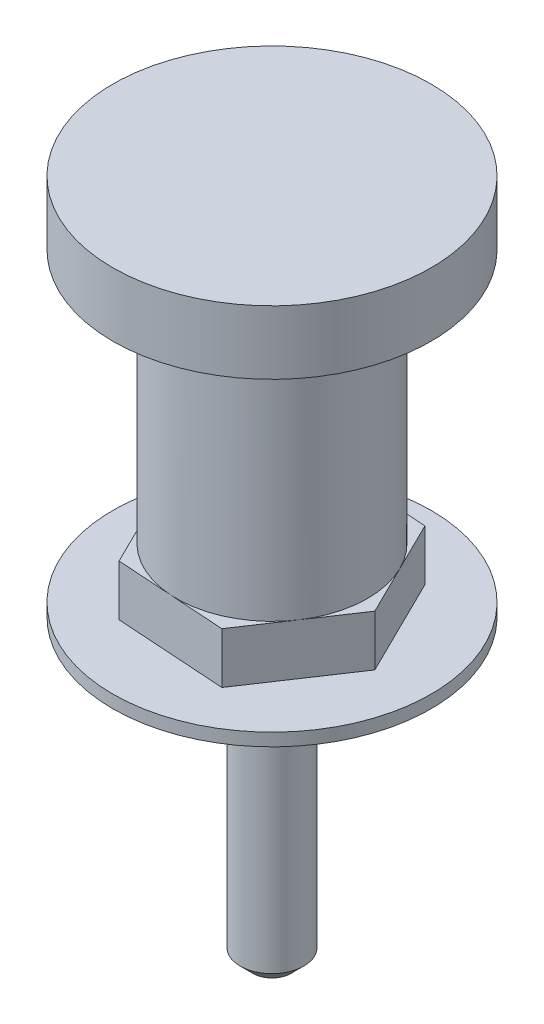
SolidWorks part; units mm, degrees
ref_plane "Front Plane" through (0, 0, 0) normal (0, 0, 1) x (1, 0, 0)
ref_plane "Top Plane" through (0, 0, 0) normal (0, 1, 0) x (1, 0, 0)
ref_plane "Right Plane" through (0, 0, 0) normal (1, 0, 0) x (0, 0, -1)
sketch "Sketch1" plane through (0, 0, 0) normal (0, 1, 0) x (1, 0, 0)
  circle A0 centre (0, 0) radius 12.5
  dimension "D1" = 25
extrude "Boss-Extrude1" add sketch "Sketch1" along normal blind 1
sketch "Sketch2" plane through (0, 1, 0) normal (0, 1, 0) x (1, 0, 0)
  line L1 (3.8307, -7.767) -> (8.6417, -0.566)
  line L2 (8.6417, -0.566) -> (4.8111, 7.2009)
  line L3 (4.8111, 7.2009) -> (-3.8307, 7.767)
  line L4 (-3.8307, 7.767) -> (-8.6417, 0.566)
  line L5 (-8.6417, 0.566) -> (-4.8111, -7.2009)
  line L6 (-4.8111, -7.2009) -> (3.8307, -7.767)
  circle A0 centre (0, 0) radius 7.5 construction
  dimension "D1" = 15
extrude "Boss-Extrude2" add sketch "Sketch2" along normal blind 4
sketch "Sketch4" plane through (0, 5, 0) normal (0, 1, 0) x (1, 0, 0)
  circle A0 centre (0, 0) radius 2.5
  dimension "D1" = 5
extrude "Boss-Extrude3" add sketch "Sketch4" against normal blind 28.5
chamfer "Chamfer1" distance 1 angle 45 1 edges at (0, -23.5, 2.5)
sketch "Sketch5" plane through (0, 5, 0) normal (0, 1, 0) x (1, 0, 0)
  circle A0 centre (0, 0) radius 7.5
  dimension "D1" = 15
extrude "Boss-Extrude4" add sketch "Sketch5" along normal blind 20
sketch "Sketch6" plane through (0, 25, 0) normal (0, 1, 0) x (1, 0, 0)
  circle A0 centre (0, 0) radius 12.5
  dimension "D1" = 25
extrude "Boss-Extrude5" add sketch "Sketch6" along normal blind 5
